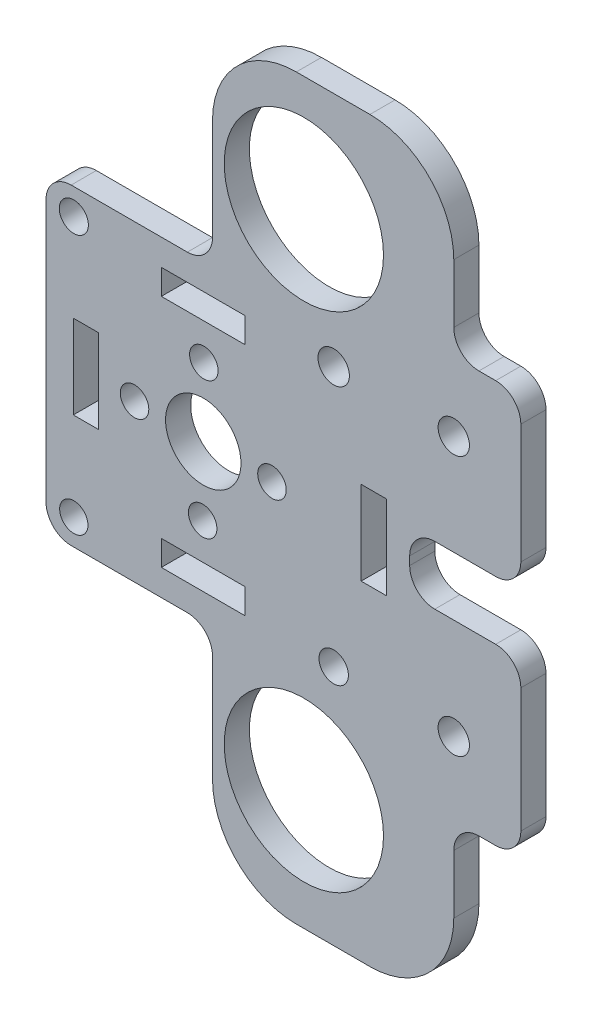
SolidWorks part; units mm, degrees
ref_plane "Front Plane" through (0, 0, 0) normal (0, 0, 1) x (1, 0, 0)
ref_plane "Top Plane" through (0, 0, 0) normal (0, 1, 0) x (1, 0, 0)
ref_plane "Right Plane" through (0, 0, 0) normal (1, 0, 0) x (0, 0, -1)
sketch "Sketch1" plane through (0, 0, 0) normal (0, 0, 1) x (1, 0, 0)
  line L0 (147.062, -92.9701) -> (147.062, -71.8565)
  line L1 (147.062, -92.9701) -> (127.2038, -92.9701)
  line L2 (127.2038, -92.9701) -> (127.2038, -111.5917)
  line L4 (147.062, -151.8871) -> (147.062, -155.8871)
  line L5 (145.9607, -111.5917) -> (157.9607, -111.5917) construction
  line L6 (157.9607, -111.5917) -> (157.9607, -81.5917) construction
  line L7 (157.9607, -111.5917) -> (157.9607, -141.5917) construction
  line L8 (147.062, -71.8565) -> (147.062, -67.8565)
  line L9 (127.2038, -111.5917) -> (127.2038, -130.2155)
  line L10 (127.2038, -130.2155) -> (147.062, -130.2155)
  line L11 (147.062, -130.2155) -> (147.062, -151.8871)
  line L13 (147.062, -67.8565) -> (175.8433, -67.8565)
  line L14 (147.062, -155.8871) -> (175.8433, -155.8871)
  line L15 (175.8433, -67.8565) -> (175.8433, -87.8565)
  line L16 (175.8433, -155.8871) -> (175.8433, -135.8871)
  line L17 (175.8433, -87.8565) -> (183.8433, -87.8565)
  line L18 (175.8433, -135.8871) -> (183.8433, -135.8871)
  line L19 (166.2936, -111.5917) -> (199.239, -111.5917) construction
  line L20 (145.9607, -111.5917) -> (131.9607, -111.5917) construction
  line L21 (145.9607, -111.5917) -> (145.9607, -97.5917) construction
  line L22 (145.9607, -111.5917) -> (145.9607, -125.5917) construction
  line L23 (157.9607, -111.5917) -> (166.2936, -111.5917) construction
  line L24 (130.4607, -106.5917) -> (133.4607, -106.5917)
  line L25 (130.4607, -106.5917) -> (130.4607, -116.5917)
  line L26 (130.4607, -116.5917) -> (133.4607, -116.5917)
  line L27 (133.4607, -106.5917) -> (133.4607, -116.5917)
  line L28 (130.4607, -106.5917) -> (133.4607, -116.5917) construction
  line L29 (130.4607, -116.5917) -> (133.4607, -106.5917) construction
  line L30 (140.9607, -99.0917) -> (150.9607, -99.0917)
  line L31 (140.9607, -99.0917) -> (140.9607, -96.0917)
  line L32 (140.9607, -96.0917) -> (150.9607, -96.0917)
  line L33 (150.9607, -99.0917) -> (150.9607, -96.0917)
  line L34 (140.9607, -99.0917) -> (150.9607, -96.0917) construction
  line L35 (140.9607, -96.0917) -> (150.9607, -99.0917) construction
  line L36 (140.9607, -127.0917) -> (150.9607, -127.0917)
  line L37 (140.9607, -127.0917) -> (140.9607, -124.0917)
  line L38 (140.9607, -124.0917) -> (150.9607, -124.0917)
  line L39 (150.9607, -127.0917) -> (150.9607, -124.0917)
  line L40 (140.9607, -127.0917) -> (150.9607, -124.0917) construction
  line L41 (140.9607, -124.0917) -> (150.9607, -127.0917) construction
  line L42 (185.7907, -111.5917) -> (185.7907, -108.0917) construction
  line L43 (164.7936, -106.5917) -> (167.7936, -106.5917)
  line L44 (164.7936, -106.5917) -> (164.7936, -116.5917)
  line L45 (164.7936, -116.5917) -> (167.7936, -116.5917)
  line L46 (167.7936, -106.5917) -> (167.7936, -116.5917)
  line L47 (164.7936, -106.5917) -> (167.7936, -116.5917) construction
  line L48 (164.7936, -116.5917) -> (167.7936, -106.5917) construction
  line L49 (185.7907, -111.5917) -> (185.7907, -115.0917) construction
  line L50 (183.8433, -87.8565) -> (183.8433, -108.0903)
  line L51 (183.8433, -108.0903) -> (170.5821, -108.0903)
  line L52 (170.5821, -108.0903) -> (170.5821, -115.0917)
  line L53 (170.5821, -115.0917) -> (183.8433, -115.0917)
  line L54 (183.8433, -115.0917) -> (183.8433, -135.8871)
  circle A0 centre (130.52, -96.082) radius 1.7379
  circle A2 centre (161.52, -96.082) radius 1.8732
  circle A3 centre (130.52, -127.1142) radius 1.6901
  circle A4 centre (161.52, -127.082) radius 1.7542
  circle A5 centre (154.1576, -111.6623) radius 1.7
  circle A6 centre (145.8901, -119.7886) radius 1.7
  circle A7 centre (137.7638, -111.5212) radius 1.7
  circle A8 centre (146.0313, -103.3948) radius 1.7
  circle A10 centre (145.9607, -111.5917) radius 4.5
  circle A12 centre (175.8433, -96.1142) radius 1.87
  circle A15 centre (157.9607, -81.5917) radius 9.5
  circle A16 centre (157.9607, -141.5917) radius 9.5
  circle A17 centre (175.8433, -127.1142) radius 1.87
  point P44 (145.9607, -111.5917)
  point P47 (106.5258, -71.8662)
  dimension "D1" = 4
  dimension "D4" = 12
  dimension "D5" = 4
  dimension "D10" = 4
  dimension "D2" = 30
  dimension "D3" = 30
  dimension "D6" = 20
  dimension "D7" = 20
  dimension "D8" = 8
  dimension "D9" = 8
  dimension "D11" = 14
  dimension "D12" = 14
  dimension "D13" = 14
  dimension "D14" = 3
  dimension "D15" = 3
  dimension "D16" = 3
  dimension "D17" = 10
  dimension "D18" = 10
  dimension "D19" = 10
  dimension "D20" = 3
  dimension "D21" = 10
  dimension "D22" = 3.5
  dimension "D23" = 3.5
extrude "Boss-Extrude1" add sketch "Sketch1" along normal blind 3
fillet "Fillet1" radius 10 4 edges at (175.8433, -155.8871, 1.5) (147.062, -155.8871, 1.5) (147.062, -67.8565, 1.5) (175.8433, -67.8565, 1.5)
fillet "Fillet2" radius 3 12 edges at (183.8433, -108.0903, 1.5) (183.8433, -115.0917, 1.5) (183.8433, -87.8565, 1.5) (183.8433, -135.8871, 1.5) (175.8433, -135.8871, 1.5) (175.8433, -87.8565, 1.5) (170.5821, -115.0917, 1.5) (170.5821, -108.0903, 1.5) (127.2038, -92.9701, 1.5) (147.062, -92.9701, 1.5) (147.062, -130.2155, 1.5) (127.2038, -130.2155, 1.5)
